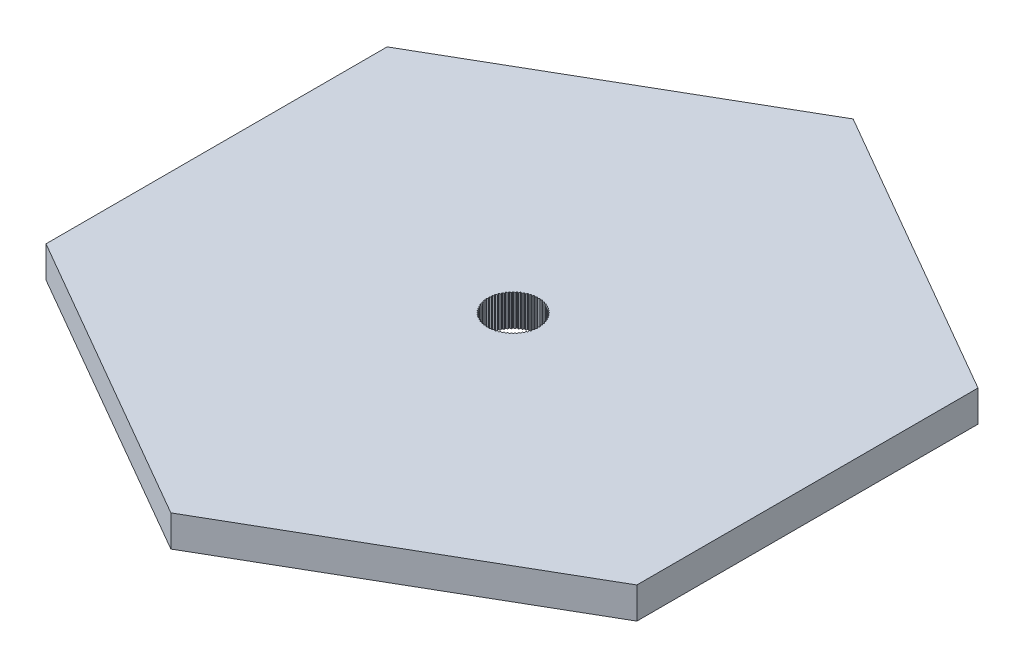
SolidWorks part; units mm, degrees
ref_plane "Front Plane" through (0, 0, 0) normal (0, 0, 1) x (1, 0, 0)
ref_plane "Top Plane" through (0, 0, 0) normal (0, 1, 0) x (1, 0, 0)
ref_plane "Right Plane" through (0, 0, 0) normal (1, 0, 0) x (0, 0, -1)
sketch "Sketch1" plane through (0, 0, 0) normal (0, 1, 0) x (1, 0, 0)
  line L1 (0, -32.6657) -> (28.2893, -16.3329)
  line L2 (28.2893, -16.3329) -> (28.2893, 16.3329)
  line L3 (28.2893, 16.3329) -> (0, 32.6657)
  line L4 (0, 32.6657) -> (-28.2893, 16.3329)
  line L5 (-28.2893, 16.3329) -> (-28.2893, -16.3329)
  line L6 (-28.2893, -16.3329) -> (0, -32.6657)
  circle A0 centre (0, 0) radius 28.2893 construction
extrude "Boss-Extrude1" add sketch "Sketch1" along normal blind 3
sketch "Sketch3" plane through (0, 3, 0) normal (0, 1, 0) x (1, 0, 0)
  line L0 (0.3935, 2.6999) -> (0.2772, 2.6244)
  line L1 (0.2772, 2.6244) -> (0.2017, 2.7407)
  line L2 (0.142, 2.7502) -> (0.0343, 2.6629)
  line L3 (0.0343, 2.6629) -> (-0.053, 2.7707)
  line L4 (-0.1133, 2.7738) -> (-0.2114, 2.6758)
  line L5 (-0.2114, 2.6758) -> (-0.3094, 2.7738)
  line L6 (-0.3698, 2.7707) -> (-0.457, 2.6629)
  line L7 (-0.457, 2.6629) -> (-0.5648, 2.7502)
  line L8 (-0.6245, 2.7407) -> (-0.7, 2.6244)
  line L9 (-0.7, 2.6244) -> (-0.8162, 2.6999)
  line L10 (-0.8746, 2.6843) -> (-0.9376, 2.5608)
  line L11 (-0.9376, 2.5608) -> (-1.0611, 2.6237)
  line L12 (-1.1175, 2.602) -> (-1.1672, 2.4726)
  line L13 (-1.1672, 2.4726) -> (-1.2966, 2.5223)
  line L14 (-1.3505, 2.4949) -> (-1.3864, 2.3609)
  line L15 (-1.3864, 2.3609) -> (-1.5203, 2.3968)
  line L16 (-1.571, 2.3639) -> (-1.5927, 2.227)
  line L17 (-1.5927, 2.227) -> (-1.7296, 2.2487)
  line L18 (-1.7766, 2.2106) -> (-1.7838, 2.0722)
  line L19 (-1.7838, 2.0722) -> (-1.9223, 2.0794)
  line L20 (-1.965, 2.0367) -> (-1.9578, 1.8982)
  line L21 (-1.9578, 1.8982) -> (-2.0962, 1.891)
  line L22 (-2.1343, 1.844) -> (-2.1126, 1.7071)
  line L23 (-2.1126, 1.7071) -> (-2.2495, 1.6854)
  line L24 (-2.2824, 1.6347) -> (-2.2465, 1.5008)
  line L25 (-2.2465, 1.5008) -> (-2.3805, 1.4649)
  line L26 (-2.4079, 1.411) -> (-2.3582, 1.2816)
  line L27 (-2.3582, 1.2816) -> (-2.4876, 1.2319)
  line L28 (-2.5093, 1.1755) -> (-2.4464, 1.052)
  line L29 (-2.4464, 1.052) -> (-2.5699, 0.989)
  line L30 (-2.5855, 0.9306) -> (-2.51, 0.8144)
  line L31 (-2.51, 0.8144) -> (-2.6263, 0.7389)
  line L32 (-2.6358, 0.6792) -> (-2.5485, 0.5714)
  line L33 (-2.5485, 0.5714) -> (-2.6562, 0.4842)
  line L34 (-2.6594, 0.4238) -> (-2.5614, 0.3258)
  line L35 (-2.5614, 0.3258) -> (-2.6594, 0.2277)
  line L36 (-2.6562, 0.1674) -> (-2.5485, 0.0801)
  line L37 (-2.5485, 0.0801) -> (-2.6358, -0.0276)
  line L38 (-2.6263, -0.0873) -> (-2.51, -0.1628)
  line L39 (-2.51, -0.1628) -> (-2.5855, -0.2791)
  line L40 (-2.5699, -0.3375) -> (-2.4464, -0.4004)
  line L41 (-2.4464, -0.4004) -> (-2.5093, -0.5239)
  line L42 (-2.4876, -0.5804) -> (-2.3582, -0.6301)
  line L43 (-2.3582, -0.6301) -> (-2.4079, -0.7595)
  line L44 (-2.3805, -0.8133) -> (-2.2465, -0.8492)
  line L45 (-2.2465, -0.8492) -> (-2.2824, -0.9831)
  line L46 (-2.2495, -1.0338) -> (-2.1126, -1.0555)
  line L47 (-2.1126, -1.0555) -> (-2.1343, -1.1925)
  line L48 (-2.0962, -1.2394) -> (-1.9578, -1.2467)
  line L49 (-1.9578, -1.2467) -> (-1.965, -1.3851)
  line L50 (-1.9223, -1.4279) -> (-1.7838, -1.4206)
  line L51 (-1.7838, -1.4206) -> (-1.7766, -1.5591)
  line L52 (-1.7296, -1.5971) -> (-1.5927, -1.5754)
  line L53 (-1.5927, -1.5754) -> (-1.571, -1.7124)
  line L54 (-1.5203, -1.7453) -> (-1.3864, -1.7094)
  line L55 (-1.3864, -1.7094) -> (-1.3505, -1.8433)
  line L56 (-1.2966, -1.8707) -> (-1.1672, -1.8211)
  line L57 (-1.1672, -1.8211) -> (-1.1175, -1.9505)
  line L58 (-1.0611, -1.9721) -> (-0.9376, -1.9092)
  line L59 (-0.9376, -1.9092) -> (-0.8746, -2.0327)
  line L60 (-0.8162, -2.0484) -> (-0.7, -1.9729)
  line L61 (-0.7, -1.9729) -> (-0.6245, -2.0891)
  line L62 (-0.5648, -2.0986) -> (-0.457, -2.0113)
  line L63 (-0.457, -2.0113) -> (-0.3698, -2.1191)
  line L64 (-0.3094, -2.1223) -> (-0.2114, -2.0242)
  line L65 (-0.2114, -2.0242) -> (-0.1133, -2.1223)
  line L66 (-0.053, -2.1191) -> (0.0343, -2.0113)
  line L67 (0.0343, -2.0113) -> (0.142, -2.0986)
  line L68 (0.2017, -2.0891) -> (0.2772, -1.9729)
  line L69 (0.2772, -1.9729) -> (0.3935, -2.0484)
  line L70 (0.4519, -2.0327) -> (0.5148, -1.9092)
  line L71 (0.5148, -1.9092) -> (0.6384, -1.9721)
  line L72 (0.6948, -1.9505) -> (0.7445, -1.8211)
  line L73 (0.7445, -1.8211) -> (0.8739, -1.8707)
  line L74 (0.9277, -1.8433) -> (0.9636, -1.7094)
  line L75 (0.9636, -1.7094) -> (1.0975, -1.7453)
  line L76 (1.1482, -1.7124) -> (1.1699, -1.5754)
  line L77 (1.1699, -1.5754) -> (1.3069, -1.5971)
  line L78 (1.3538, -1.5591) -> (1.3611, -1.4206)
  line L79 (1.3611, -1.4206) -> (1.4995, -1.4279)
  line L80 (1.5423, -1.3851) -> (1.535, -1.2467)
  line L81 (1.535, -1.2467) -> (1.6735, -1.2394)
  line L82 (1.7115, -1.1925) -> (1.6898, -1.0555)
  line L83 (1.6898, -1.0555) -> (1.8268, -1.0338)
  line L84 (1.8597, -0.9831) -> (1.8238, -0.8492)
  line L85 (1.8238, -0.8492) -> (1.9577, -0.8133)
  line L86 (1.9851, -0.7595) -> (1.9355, -0.6301)
  line L87 (1.9355, -0.6301) -> (2.0649, -0.5804)
  line L88 (2.0866, -0.5239) -> (2.0236, -0.4004)
  line L89 (2.0236, -0.4004) -> (2.1471, -0.3375)
  line L90 (2.1628, -0.2791) -> (2.0873, -0.1628)
  line L91 (2.0873, -0.1628) -> (2.2036, -0.0873)
  line L92 (2.213, -0.0276) -> (2.1258, 0.0801)
  line L93 (2.1258, 0.0801) -> (2.2335, 0.1674)
  line L94 (2.2367, 0.2277) -> (2.1386, 0.3258)
  line L95 (2.1386, 0.3258) -> (2.2367, 0.4238)
  line L96 (2.2335, 0.4842) -> (2.1258, 0.5714)
  line L97 (2.1258, 0.5714) -> (2.213, 0.6792)
  line L98 (2.2036, 0.7389) -> (2.0873, 0.8144)
  line L99 (2.0873, 0.8144) -> (2.1628, 0.9306)
  line L100 (2.1471, 0.989) -> (2.0236, 1.052)
  line L101 (2.0236, 1.052) -> (2.0866, 1.1755)
  line L102 (2.0649, 1.2319) -> (1.9355, 1.2816)
  line L103 (1.9355, 1.2816) -> (1.9851, 1.411)
  line L104 (1.9577, 1.4649) -> (1.8238, 1.5008)
  line L105 (1.8238, 1.5008) -> (1.8597, 1.6347)
  line L106 (1.8268, 1.6854) -> (1.6898, 1.7071)
  line L107 (1.6898, 1.7071) -> (1.7115, 1.844)
  line L108 (1.6735, 1.891) -> (1.535, 1.8982)
  line L109 (1.535, 1.8982) -> (1.5423, 2.0367)
  line L110 (1.4995, 2.0794) -> (1.3611, 2.0722)
  line L111 (1.3611, 2.0722) -> (1.3538, 2.2106)
  line L112 (1.3069, 2.2487) -> (1.1699, 2.227)
  line L113 (1.1699, 2.227) -> (1.1482, 2.3639)
  line L114 (1.0975, 2.3968) -> (0.9636, 2.3609)
  line L115 (0.9636, 2.3609) -> (0.9277, 2.4949)
  line L116 (0.8739, 2.5223) -> (0.7445, 2.4726)
  line L117 (0.7445, 2.4726) -> (0.6948, 2.602)
  line L118 (0.6384, 2.6237) -> (0.5148, 2.5608)
  line L119 (0.5148, 2.5608) -> (0.4519, 2.6843)
  arc A0 (0.2017, 2.7407) -> (0.142, 2.7502) centre (-0.2114, 0.3258) ccw
  arc A1 (-0.053, 2.7707) -> (-0.1133, 2.7738) centre (-0.2114, 0.3258) ccw
  arc A2 (-0.3094, 2.7738) -> (-0.3698, 2.7707) centre (-0.2114, 0.3258) ccw
  arc A3 (-0.5648, 2.7502) -> (-0.6245, 2.7407) centre (-0.2114, 0.3258) ccw
  arc A4 (-0.8162, 2.6999) -> (-0.8746, 2.6843) centre (-0.2114, 0.3258) ccw
  arc A5 (-1.0611, 2.6237) -> (-1.1175, 2.602) centre (-0.2114, 0.3258) ccw
  arc A6 (-1.2966, 2.5223) -> (-1.3505, 2.4949) centre (-0.2114, 0.3258) ccw
  arc A7 (-1.5203, 2.3968) -> (-1.571, 2.3639) centre (-0.2114, 0.3258) ccw
  arc A8 (-1.7296, 2.2487) -> (-1.7766, 2.2106) centre (-0.2114, 0.3258) ccw
  arc A9 (-1.9223, 2.0794) -> (-1.965, 2.0367) centre (-0.2114, 0.3258) ccw
  arc A10 (-2.0962, 1.891) -> (-2.1343, 1.844) centre (-0.2114, 0.3258) ccw
  arc A11 (-2.2495, 1.6854) -> (-2.2824, 1.6347) centre (-0.2114, 0.3258) ccw
  arc A12 (-2.3805, 1.4649) -> (-2.4079, 1.411) centre (-0.2114, 0.3258) ccw
  arc A13 (-2.4876, 1.2319) -> (-2.5093, 1.1755) centre (-0.2114, 0.3258) ccw
  arc A14 (-2.5699, 0.989) -> (-2.5855, 0.9306) centre (-0.2114, 0.3258) ccw
  arc A15 (-2.6263, 0.7389) -> (-2.6358, 0.6792) centre (-0.2114, 0.3258) ccw
  arc A16 (-2.6562, 0.4842) -> (-2.6594, 0.4238) centre (-0.2114, 0.3258) ccw
  arc A17 (-2.6594, 0.2277) -> (-2.6562, 0.1674) centre (-0.2114, 0.3258) ccw
  arc A18 (-2.6358, -0.0276) -> (-2.6263, -0.0873) centre (-0.2114, 0.3258) ccw
  arc A19 (-2.5855, -0.2791) -> (-2.5699, -0.3375) centre (-0.2114, 0.3258) ccw
  arc A20 (-2.5093, -0.5239) -> (-2.4876, -0.5804) centre (-0.2114, 0.3258) ccw
  arc A21 (-2.4079, -0.7595) -> (-2.3805, -0.8133) centre (-0.2114, 0.3258) ccw
  arc A22 (-2.2824, -0.9831) -> (-2.2495, -1.0338) centre (-0.2114, 0.3258) ccw
  arc A23 (-2.1343, -1.1925) -> (-2.0962, -1.2394) centre (-0.2114, 0.3258) ccw
  arc A24 (-1.965, -1.3851) -> (-1.9223, -1.4279) centre (-0.2114, 0.3258) ccw
  arc A25 (-1.7766, -1.5591) -> (-1.7296, -1.5971) centre (-0.2114, 0.3258) ccw
  arc A26 (-1.571, -1.7124) -> (-1.5203, -1.7453) centre (-0.2114, 0.3258) ccw
  arc A27 (-1.3505, -1.8433) -> (-1.2966, -1.8707) centre (-0.2114, 0.3258) ccw
  arc A28 (-1.1175, -1.9505) -> (-1.0611, -1.9721) centre (-0.2114, 0.3258) ccw
  arc A29 (-0.8746, -2.0327) -> (-0.8162, -2.0484) centre (-0.2114, 0.3258) ccw
  arc A30 (-0.6245, -2.0891) -> (-0.5648, -2.0986) centre (-0.2114, 0.3258) ccw
  arc A31 (-0.3698, -2.1191) -> (-0.3094, -2.1223) centre (-0.2114, 0.3258) ccw
  arc A32 (-0.1133, -2.1223) -> (-0.053, -2.1191) centre (-0.2114, 0.3258) ccw
  arc A33 (0.142, -2.0986) -> (0.2017, -2.0891) centre (-0.2114, 0.3258) ccw
  arc A34 (0.3935, -2.0484) -> (0.4519, -2.0327) centre (-0.2114, 0.3258) ccw
  arc A35 (0.6384, -1.9721) -> (0.6948, -1.9505) centre (-0.2114, 0.3258) ccw
  arc A36 (0.8739, -1.8707) -> (0.9277, -1.8433) centre (-0.2114, 0.3258) ccw
  arc A37 (1.0975, -1.7453) -> (1.1482, -1.7124) centre (-0.2114, 0.3258) ccw
  arc A38 (1.3069, -1.5971) -> (1.3538, -1.5591) centre (-0.2114, 0.3258) ccw
  arc A39 (1.4995, -1.4279) -> (1.5423, -1.3851) centre (-0.2114, 0.3258) ccw
  arc A40 (1.6735, -1.2394) -> (1.7115, -1.1925) centre (-0.2114, 0.3258) ccw
  arc A41 (1.8268, -1.0338) -> (1.8597, -0.9831) centre (-0.2114, 0.3258) ccw
  arc A42 (1.9577, -0.8133) -> (1.9851, -0.7595) centre (-0.2114, 0.3258) ccw
  arc A43 (2.0649, -0.5804) -> (2.0866, -0.5239) centre (-0.2114, 0.3258) ccw
  arc A44 (2.1471, -0.3375) -> (2.1628, -0.2791) centre (-0.2114, 0.3258) ccw
  arc A45 (2.2036, -0.0873) -> (2.213, -0.0276) centre (-0.2114, 0.3258) ccw
  arc A46 (2.2335, 0.1674) -> (2.2367, 0.2277) centre (-0.2114, 0.3258) ccw
  arc A47 (2.2367, 0.4238) -> (2.2335, 0.4842) centre (-0.2114, 0.3258) ccw
  arc A48 (2.213, 0.6792) -> (2.2036, 0.7389) centre (-0.2114, 0.3258) ccw
  arc A49 (2.1628, 0.9306) -> (2.1471, 0.989) centre (-0.2114, 0.3258) ccw
  arc A50 (2.0866, 1.1755) -> (2.0649, 1.2319) centre (-0.2114, 0.3258) ccw
  arc A51 (1.9851, 1.411) -> (1.9577, 1.4649) centre (-0.2114, 0.3258) ccw
  arc A52 (1.8597, 1.6347) -> (1.8268, 1.6854) centre (-0.2114, 0.3258) ccw
  arc A53 (1.7115, 1.844) -> (1.6735, 1.891) centre (-0.2114, 0.3258) ccw
  arc A54 (1.5423, 2.0367) -> (1.4995, 2.0794) centre (-0.2114, 0.3258) ccw
  arc A55 (1.3538, 2.2106) -> (1.3069, 2.2487) centre (-0.2114, 0.3258) ccw
  arc A56 (1.1482, 2.3639) -> (1.0975, 2.3968) centre (-0.2114, 0.3258) ccw
  arc A57 (0.9277, 2.4949) -> (0.8739, 2.5223) centre (-0.2114, 0.3258) ccw
  arc A58 (0.6948, 2.602) -> (0.6384, 2.6237) centre (-0.2114, 0.3258) ccw
  arc A59 (0.4519, 2.6843) -> (0.3935, 2.6999) centre (-0.2114, 0.3258) ccw
extrude "Cut-Extrude1" cut sketch "Sketch3" against normal blind 10
